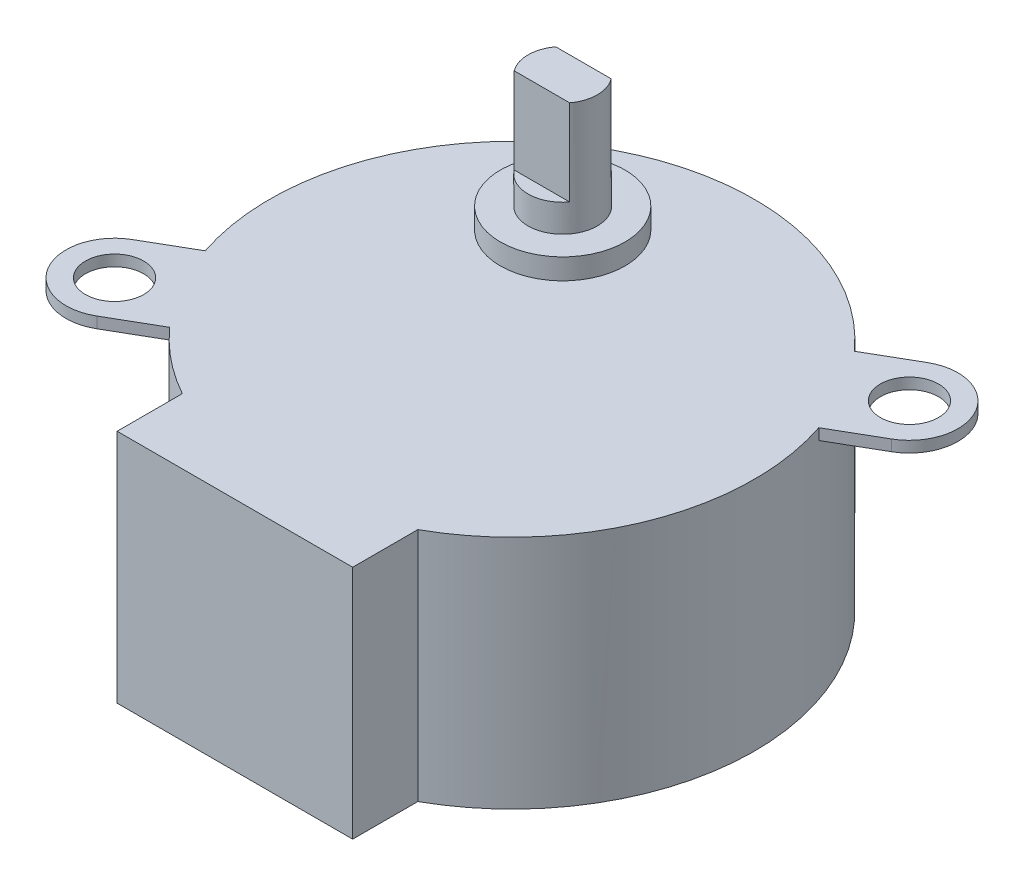
SolidWorks part; units mm, degrees
ref_plane "Front Plane" through (0, 0, 0) normal (0, 0, 1) x (1, 0, 0)
ref_plane "Top Plane" through (0, 0, 0) normal (0, 1, 0) x (1, 0, 0)
ref_plane "Right Plane" through (0, 0, 0) normal (1, 0, 0) x (0, 0, -1)
sketch "Sketch1" plane through (0, 0, 0) normal (0, 1, 0) x (1, 0, 0)
  line L2 (-8.5, -20) -> (8.5, -20)
  line L3 (-19.9365, -7.4689) -> (-16.5992, -5.5421)
  line L4 (-16.4365, -13.5311) -> (-13.0992, -11.6043)
  line L5 (16.5992, 5.5421) -> (19.9365, 7.4689)
  line L6 (13.0992, 11.6043) -> (16.4365, 13.5311)
  line L7 (-8.5, -15.2971) -> (-8.5, -20)
  line L8 (8.5, -15.2971) -> (8.5, -20)
  arc A0 (8.5, -15.2971) -> (16.5992, 5.5421) centre (0, 0) ccw
  circle A1 centre (-18.1865, -10.5) radius 2.1
  circle A2 centre (18.1865, 10.5) radius 2.1
  arc A3 (-19.9365, -7.4689) -> (-16.4365, -13.5311) centre (-18.1865, -10.5) ccw
  arc A4 (19.9365, 7.4689) -> (16.4365, 13.5311) centre (18.1865, 10.5) ccw
  arc A6 (-13.0992, -11.6043) -> (-8.5, -15.2971) centre (0, 0) ccw
  arc A7 (13.0992, 11.6043) -> (-16.5992, -5.5421) centre (0, 0) ccw
  point P6 (0, 0)
  point P9 (0, 0)
  point P12 (0, 0)
  dimension "D1" = 35
  dimension "D4" = 4.2
  dimension "D5" = 4.2
  dimension "D3" = 7
  dimension "D8" = 7
  dimension "D6" = 21
  dimension "D7" = 21
  dimension "D9" = 17
extrude "Boss-Extrude2" add sketch "Sketch1" along normal blind 17
sketch "Sketch4" plane through (0, 17, 0) normal (0, 1, 0) x (1, 0, 0)
  circle A0 centre (-5, 8.6603) radius 4.5
  dimension "D3" = 9
extrude "Boss-Extrude3" add sketch "Sketch4" along normal blind 1.5
sketch "Sketch5" plane through (0, 18.5, 0) normal (0, 1, 0) x (1, 0, 0)
  circle A0 centre (-5, 8.6603) radius 2.5
  dimension "D1" = 5
extrude "Boss-Extrude4" add sketch "Sketch5" along normal blind 2
sketch "Sketch8" plane through (0, 0, 0) normal (0, -1, 0) x (1, 0, 0)
  line L0 (-16.5992, 5.5421) -> (-19.9365, 7.4689) construction
  line L1 (-16.4365, 13.5311) -> (-13.0992, 11.6043) construction
  line L2 (-16.5992, 5.5421) -> (-19.9365, 7.4689)
  line L3 (-16.4365, 13.5311) -> (-13.0992, 11.6043)
  line L4 (0, 0) -> (3.8075, 6.5948)
  line L5 (19.9365, -7.4689) -> (16.5992, -5.5421)
  line L6 (13.0992, -11.6043) -> (16.4365, -13.5311)
  circle A0 centre (-18.1865, 10.5) radius 2.1 construction
  arc A1 (-16.4365, 13.5311) -> (-19.9365, 7.4689) centre (-18.1865, 10.5) ccw construction
  circle A2 centre (-18.1865, 10.5) radius 2.1
  arc A3 (-16.4365, 13.5311) -> (-19.9365, 7.4689) centre (-18.1865, 10.5) ccw
  arc A4 (-13.0992, 11.6043) -> (-16.5992, 5.5421) centre (0, 0) ccw
  arc A5 (16.5992, -5.5421) -> (13.0992, -11.6043) centre (0, 0) cw
  arc A6 (19.9365, -7.4689) -> (16.4365, -13.5311) centre (18.1865, -10.5) cw
  circle A7 centre (18.1865, -10.5) radius 2.1
  line M4 (-13.0992, 11.6043) -> (-16.4365, 13.5311)
  arc M5 (-16.4365, 13.5311) -> (-19.9365, 7.4689) centre (-18.1865, 10.5) ccw
  line M6 (-19.9365, 7.4689) -> (-16.5992, 5.5421)
  line M8 (13.0992, -11.6043) -> (16.4365, -13.5311)
  arc M9 (16.4365, -13.5311) -> (19.9365, -7.4689) centre (18.1865, -10.5) ccw
  line M10 (19.9365, -7.4689) -> (16.5992, -5.5421)
  circle M15 centre (-18.1865, 10.5) radius 2.1
  circle M16 centre (18.1865, -10.5) radius 2.1
extrude "Cut-Extrude1" cut sketch "Sketch8" against normal blind 16.2 contours A5 M10 M8 M9 M16 | A4 M4 M5 M6 M15
sketch "Sketch9" plane through (0, 20.5, 0) normal (0, 1, 0) x (1, 0, 0)
  line L1 (-7, 7.1603) -> (-3, 7.1603)
  line L2 (-7, 10.1603) -> (-3, 10.1603)
  arc A0 (-7, 10.1603) -> (-7, 7.1603) centre (-5, 8.6603) ccw
  circle A1 centre (-5, 8.6603) radius 2.5
  arc A2 (-3, 7.1603) -> (-3, 10.1603) centre (-5, 8.6603) ccw
  point P5 (-5, 8.6603)
  dimension "D1" = 0
extrude "Boss-Extrude6" add sketch "Sketch9" along normal blind 6.2
